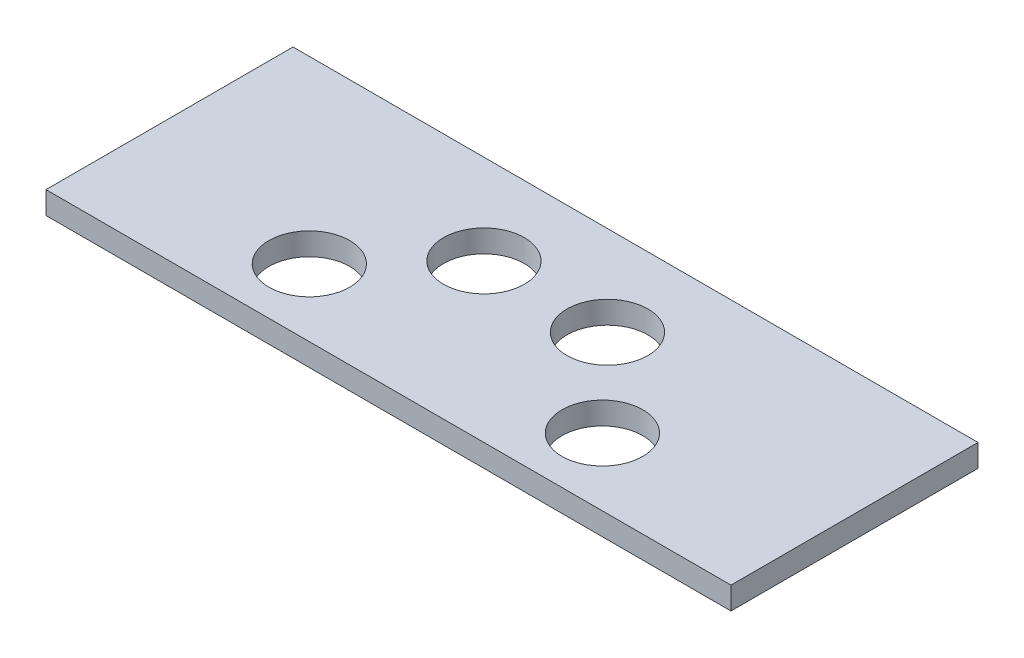
SolidWorks part; units mm, degrees
ref_plane "Front Plane" through (0, 0, 0) normal (0, 0, 1) x (1, 0, 0)
ref_plane "Top Plane" through (0, 0, 0) normal (0, 1, 0) x (1, 0, 0)
ref_plane "Right Plane" through (0, 0, 0) normal (1, 0, 0) x (0, 0, -1)
sketch "Sketch1" plane through (0, 0, 0) normal (0, 1, 0) x (1, 0, 0)
  line L1 (-18.3949, 8.1355) -> (12.1051, 8.1355)
  line L2 (-18.3949, 8.1355) -> (-18.3949, -2.8645)
  line L3 (-18.3949, -2.8645) -> (12.1051, -2.8645)
  line L4 (12.1051, 8.1355) -> (12.1051, -2.8645)
  circle A0 centre (-5.8949, 4.1355) radius 1.8
  circle A1 centre (-0.3949, 4.1355) radius 1.8
  circle A2 centre (-9.6699, 0.1355) radius 1.8
  circle A3 centre (3.38, 0.1355) radius 1.8
  dimension "D9" = 3.6
  dimension "D1" = 30.5
  dimension "D2" = 11
  dimension "D3" = 5.5
  dimension "D4" = 5.5
  dimension "D5" = 5.5
  dimension "D6" = 4
  dimension "D7" = 8
  dimension "D8" = 18
extrude "Boss-Extrude1" add sketch "Sketch1" along normal blind 1
